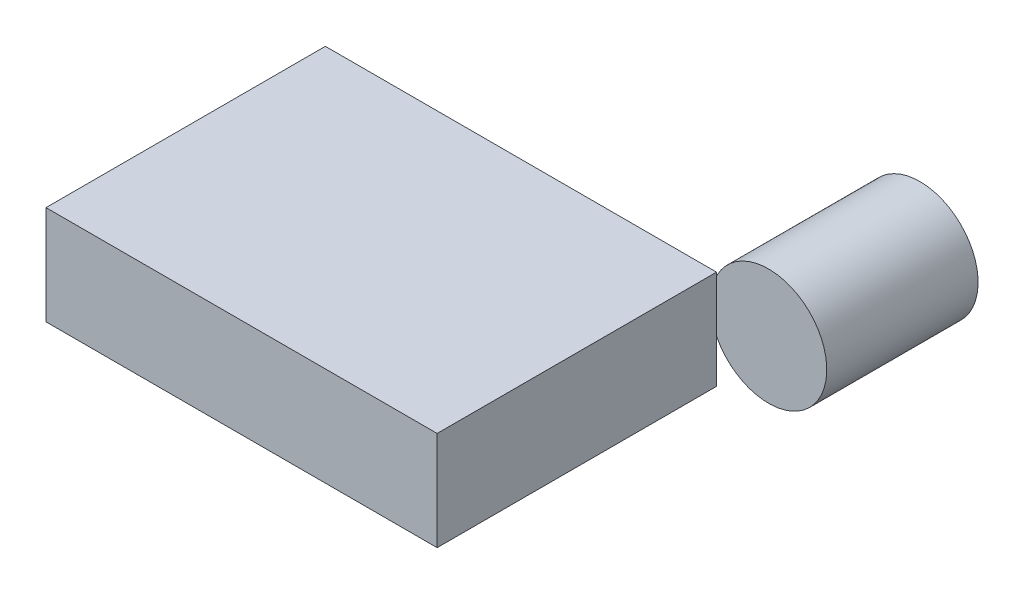
SolidWorks part; units mm, degrees
ref_plane "Front Plane" through (0, 0, 0) normal (0, 0, 1) x (1, 0, 0)
ref_plane "Top Plane" through (0, 0, 0) normal (0, 1, 0) x (1, 0, 0)
ref_plane "Right Plane" through (0, 0, 0) normal (1, 0, 0) x (0, 0, -1)
sketch "Sketch1" plane through (0, 0, 0) normal (0, 1, 0) x (1, 0, 0)
  line L1 (-16.8, -12) -> (16.8, -12)
  line L2 (-16.8, -12) -> (-16.8, 12)
  line L3 (-16.8, 12) -> (16.8, 12)
  line L4 (16.8, -12) -> (16.8, 12)
  line L5 (-16.8, -12) -> (16.8, 12) construction
  line L6 (-16.8, 12) -> (16.8, -12) construction
  point P0 (0, 0)
  dimension "D1" = 33.6
  dimension "D2" = 24
extrude "Boss-Extrude1" add sketch "Sketch1" along normal blind 8.5
sketch "Sketch2" plane through (0, 0, -12) normal (0, 0, -1) x (-1, 0, 0)
  circle A0 centre (-21.2711, 5.9753) radius 5
  dimension "D1" = 10
extrude "Boss-Extrude2" add sketch "Sketch2" along normal blind 13 separate body
